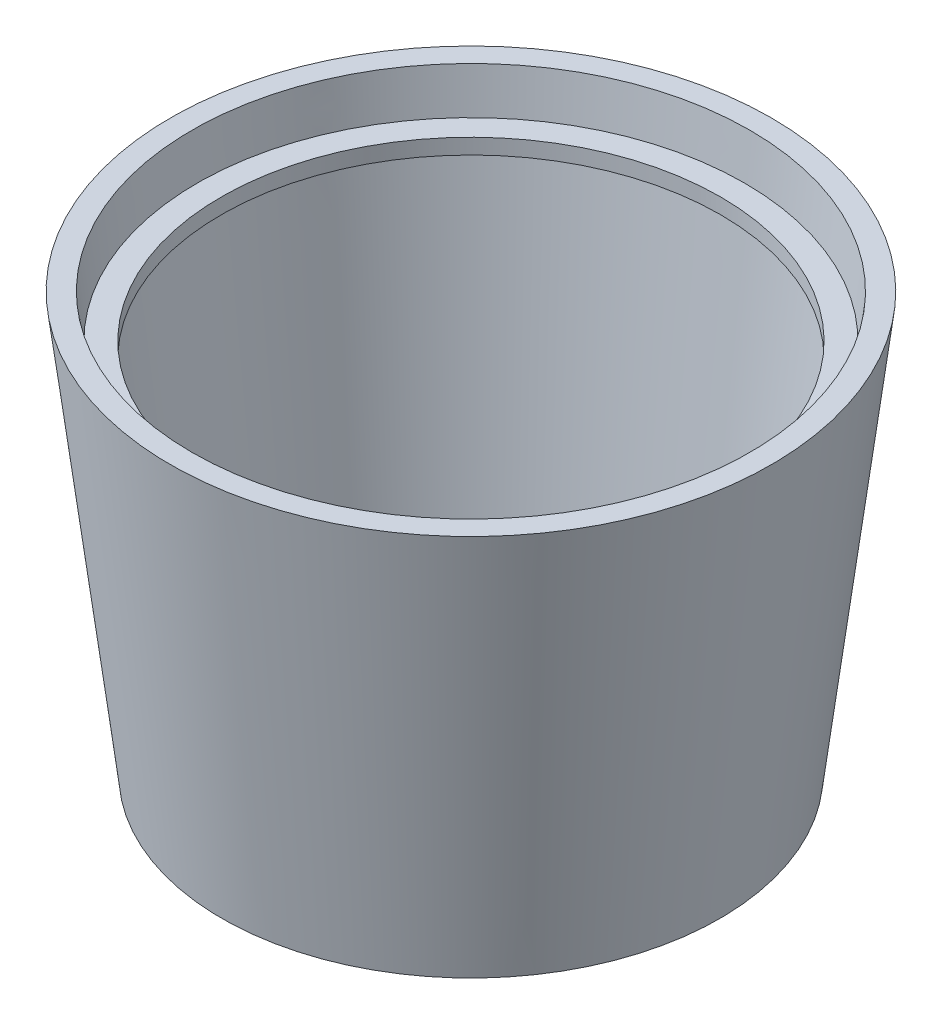
SolidWorks part; units mm, degrees
ref_plane "前视基准面" through (0, 0, 0) normal (0, 0, 1) x (1, 0, 0)
ref_plane "上视基准面" through (0, 0, 0) normal (0, 1, 0) x (1, 0, 0)
ref_plane "右视基准面" through (0, 0, 0) normal (1, 0, 0) x (0, 0, -1)
sketch "草图1" plane through (0, 0, 0) normal (0, 0, 1) x (1, 0, 0)
  line L0 (-281.0539, 0) -> (-210.9695, 0)
  line L1 (-281.0539, 0) -> (-281.0539, 14)
  line L2 (-210.9695, 0) -> (-99.2603, 909.7985)
  line L3 (-99.2603, 909.7985) -> (-145.7568, 909.7985)
  line L4 (-145.7568, 909.7985) -> (-157.2713, 816.0209)
  line L5 (-157.2713, 816.0209) -> (-209.3997, 816.0209)
  line L6 (-209.3997, 816.0209) -> (-209.3997, 782.5475)
  line L7 (-152.7855, 782.5475) -> (-247.1513, 14)
  line L8 (-209.3997, 782.5475) -> (-152.7855, 782.5475)
  line L9 (-281.0539, 14) -> (-247.1513, 14)
  line L10 (-281.0539, 0) -> (-752, 0) construction
  line L11 (-752, 0) -> (-752, 109.4948) construction
  point P2 (-387.2712, 668.0374)
  point P3 (0, 0)
  point P14 (-145.7568, 909.7985)
  point P15 (-209.3997, 816.0209)
revolve "旋转1" add sketch "草图1" angle 360 about L11
